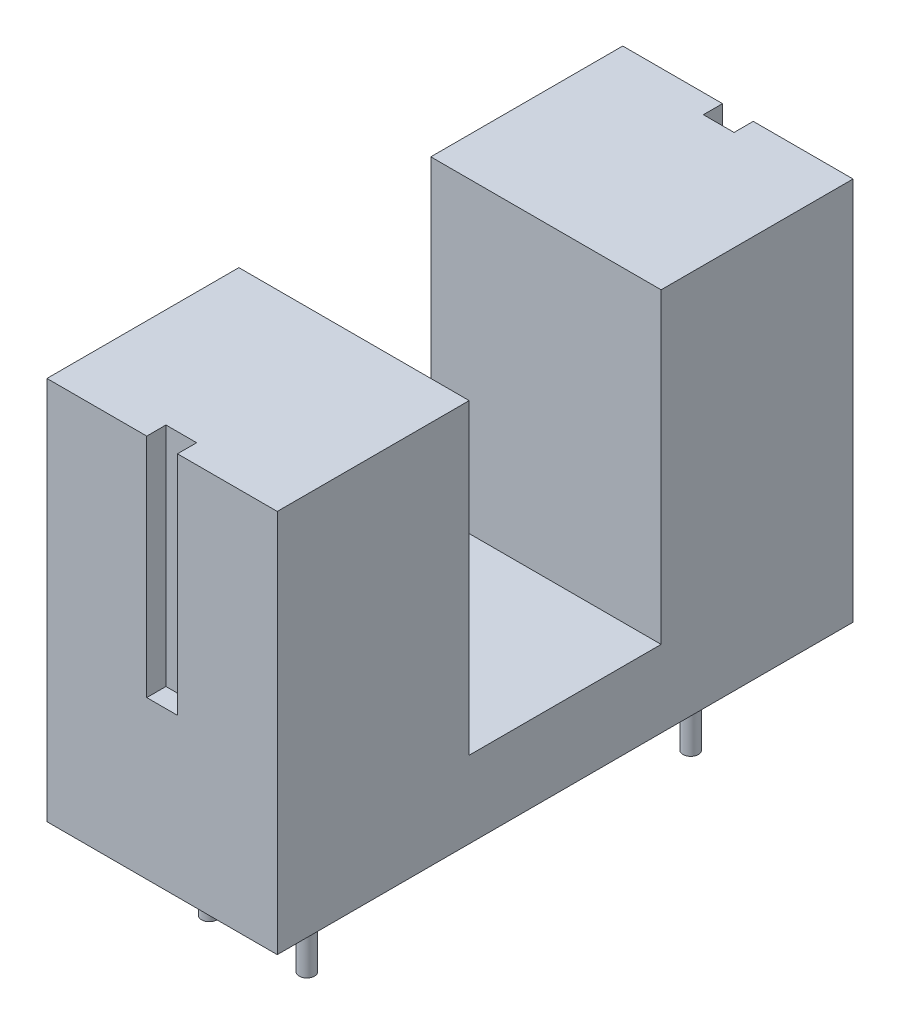
SolidWorks part; units mm, degrees
ref_plane "Front Plane" through (0, 0, 0) normal (0, 0, 1) x (1, 0, 0)
ref_plane "Top Plane" through (0, 0, 0) normal (0, 1, 0) x (1, 0, 0)
ref_plane "Right Plane" through (0, 0, 0) normal (1, 0, 0) x (0, 0, -1)
sketch "Sketch1" plane through (0, 0, 0) normal (1, 0, 0) x (0, 0, -1)
  line L0 (-50, 0) -> (50, 0) construction
  line L1 (-7.5, -6.8) -> (-7.5, 3.2)
  line L2 (-7.5, 3.2) -> (-2.5, 3.2)
  line L3 (-2.5, 3.2) -> (-2.5, -4.8)
  line L4 (7.5, -6.8) -> (-7.5, -6.8)
  line L5 (0, 48.0453) -> (0, -48.0453) construction
  line L6 (-2.5, -4.8) -> (2.5, -4.8)
  line L7 (2.5, 3.2) -> (2.5, -4.8)
  line L8 (7.5, 3.2) -> (2.5, 3.2)
  line L9 (7.5, -6.8) -> (7.5, 3.2)
  point P3 (0, 0)
  point P13 (0, -4.8)
  point P14 (0, -6.8)
  dimension "D1" = 100
  dimension "D2" = 2.5
  dimension "D3" = 3.2
  dimension "D4" = 6.8
  dimension "D5" = 7.5
  dimension "D6" = 2
extrude "Boss-Extrude1" add sketch "Sketch1" along normal blind 6
sketch "Sketch2" plane through (0, 0, -7.5) normal (0, 0, -1) x (-1, 0, 0)
  line L0 (-6, 3.2) -> (0, 3.2) construction
  line L1 (-3.4, 3.2) -> (-2.6, 3.2)
  line L2 (-3.4, 3.2) -> (-3.4, -2.7)
  line L3 (-3.4, -2.7) -> (-2.6, -2.7)
  line L4 (-2.6, 3.2) -> (-2.6, -2.7)
  line L5 (-3, -6.8) -> (-3, 3.2) construction
  line L6 (-6, -6.8) -> (0, -6.8) construction
  point P10 (-3, -2.7)
  dimension "D1" = 0.8
  dimension "D2" = 5.9
extrude "Cut-Extrude1" cut sketch "Sketch2" against normal blind 0.5
ref_plane "Plane1" through (0, 0, 0) normal (0, 0, 1) x (1, 0, 0)
mirror "Mirror1" about plane through (0, 0, 0) normal (0, 0, 1) of "Cut-Extrude1"
sketch "Sketch3" plane through (0, -6.8, 0) normal (0, -1, 0) x (1, 0, 0)
  line L0 (0, 0) -> (6, 0) construction
  line L3 (1.73, -5) -> (1.73, 0) construction
  line L4 (6.4088, 0) -> (-6.4088, 0) construction
  line L5 (6, 7.5) -> (6, -7.5) construction
  line L6 (3, -7.5) -> (3, 7.5) construction
  line L7 (6, -7.5) -> (0, -7.5) construction
  line L8 (6, 7.5) -> (0, 7.5) construction
  circle A0 centre (1.73, -5) radius 0.2
  circle A1 centre (4.27, -5) radius 0.2
  circle A2 centre (4.27, 5) radius 0.2
  circle A3 centre (1.73, 5) radius 0.2
  dimension "D1" = 5
  dimension "D3" = 0.4
  dimension "D2" = 2.54
extrude "Boss-Extrude2" add sketch "Sketch3" along normal blind 2.5
